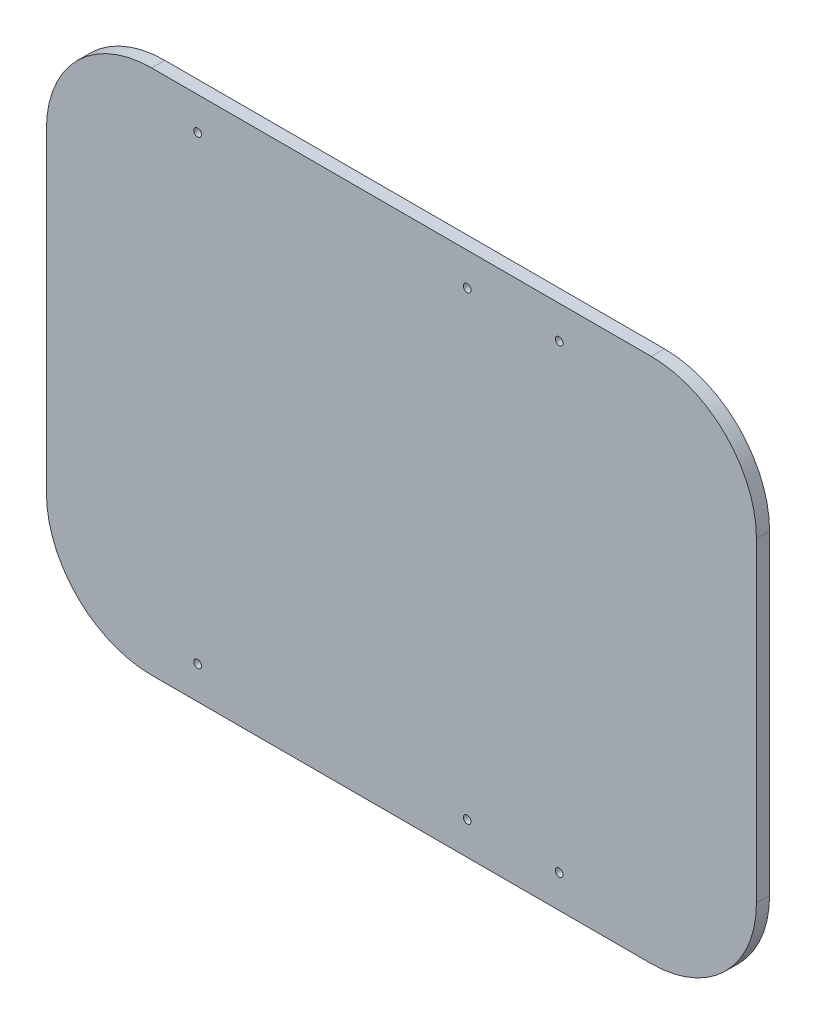
SolidWorks part; units mm, degrees
ref_plane "Front Plane" through (0, 0, 0) normal (0, 0, 1) x (1, 0, 0)
ref_plane "Top Plane" through (0, 0, 0) normal (0, 1, 0) x (1, 0, 0)
ref_plane "Right Plane" through (0, 0, 0) normal (1, 0, 0) x (0, 0, -1)
sketch "Sketch2" plane through (0, 0, 0) normal (0, 0, 1) x (1, 0, 0)
  line L0 (-135, 0) -> (135, 0)
  line L1 (-95, 100) -> (95, 100)
  line L2 (-135, 60) -> (-135, -60)
  line L3 (-95, -100) -> (95, -100)
  line L4 (135, 60) -> (135, -60)
  line L5 (-135, 100) -> (135, -100) construction
  line L6 (-135, -100) -> (135, 100) construction
  line L7 (-95, 100) -> (-95, -100)
  line L8 (95, 100) -> (95, -100)
  line L9 (-95, -82.5) -> (95, -82.5)
  line L10 (-95, 100) -> (95, 100)
  line L11 (-95, 100) -> (-95, 82.5)
  line L12 (-95, 82.5) -> (95, 82.5)
  line L13 (95, 100) -> (95, 82.5)
  line L14 (-95, 82.5) -> (95, 82.5)
  line L15 (-95, 82.5) -> (-95, 87.5)
  line L16 (-95, 87.5) -> (95, 87.5)
  line L17 (95, 82.5) -> (95, 87.5)
  line L18 (-95, -87.5) -> (95, -87.5)
  arc A0 (135, 60) -> (95, 100) centre (95, 60) ccw
  arc A1 (135, -60) -> (95, -100) centre (95, -60) cw
  arc A2 (-135, -60) -> (-95, -100) centre (-95, -60) ccw
  arc A3 (-95, 100) -> (-135, 60) centre (-95, 60) ccw
  circle A4 centre (-77.5, 87.5) radius 1.475
  circle A5 centre (25, 87.5) radius 1.475
  circle A6 centre (60, 87.5) radius 1.475
  circle A7 centre (60, -87.5) radius 1.475
  circle A8 centre (25, -87.5) radius 1.475
  circle A9 centre (-77.5, -87.5) radius 1.475
  point P0 (0, 0)
  point P24 (-77.5, 87.5)
  point P25 (25, 87.5)
  point P26 (60, 87.5)
  dimension "D3" = 40
  dimension "D9" = 2.95
  dimension "D1" = 270
  dimension "D2" = 200
  dimension "D4" = 17.5
  dimension "D5" = 5
  dimension "D6" = 17.5
  dimension "D7" = 35
  dimension "D8" = 35
extrude "Boss-Extrude1" add sketch "Sketch2" along normal blind 5 contours L12 L7 L0 L8 | L7 A3 L2 L0 L11 | L2 A2 L7 L0 | L7 L9 L8 L0 | A1 L4 L0 L8 | L4 A0 L8 L13 L0 | A6 L16 L8 L1 L7 A4 A5 | A6 L16 A5 A4 L11 L12 L13 | L18 A9 L7 L3 L8 A7 A8 | L18 A9 A8 A7 L8 L9 L7
